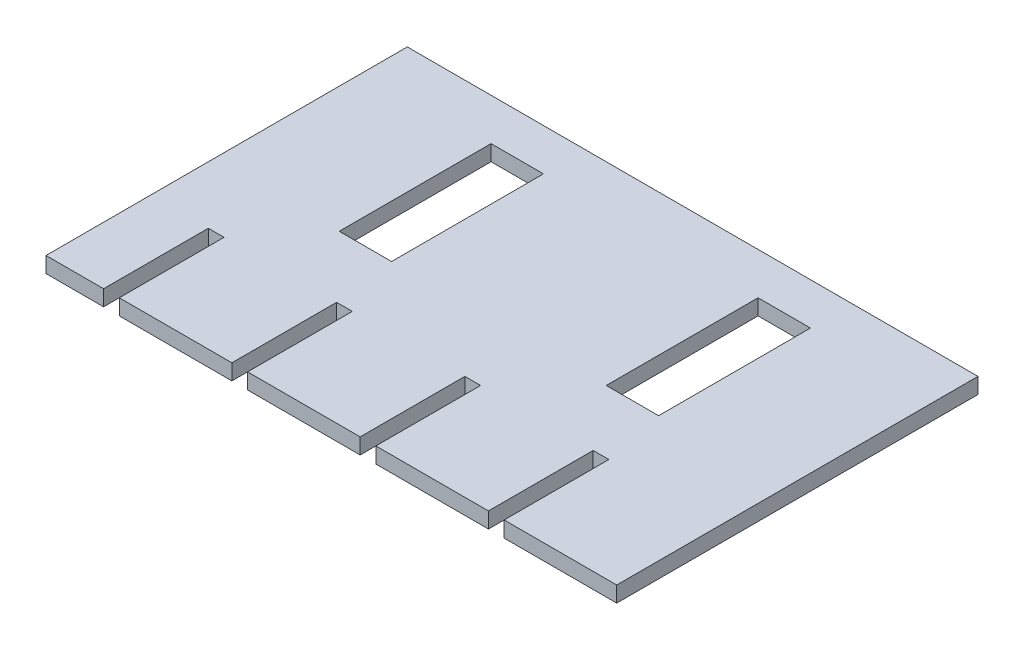
SolidWorks part; units mm, degrees
ref_plane "Front Plane" through (0, 0, 0) normal (0, 0, 1) x (1, 0, 0)
ref_plane "Top Plane" through (0, 0, 0) normal (0, 1, 0) x (1, 0, 0)
ref_plane "Right Plane" through (0, 0, 0) normal (1, 0, 0) x (0, 0, -1)
sketch "Sketch1" plane through (0, 0, 0) normal (0, 1, 0) x (1, 0, 0)
  line L1 (-27.25, 17.25) -> (27.25, 17.25)
  line L2 (-27.25, 17.25) -> (-27.25, -17.25)
  line L3 (-27.25, -17.25) -> (27.25, -17.25)
  line L4 (27.25, 17.25) -> (27.25, -17.25)
  line L5 (-27.25, 17.25) -> (27.25, -17.25) construction
  line L6 (-27.25, -17.25) -> (27.25, 17.25) construction
  point P0 (0, 0)
extrude "Boss-Extrude1" add sketch "Sketch1" along normal blind 1.5
sketch "Sketch2" plane through (0, 1.5, 0) normal (0, 1, 0) x (1, 0, 0)
  line L0 (0, 17.25) -> (0, 6)
  line L1 (27.25, 17.25) -> (-27.25, 17.25) construction
sketch "Sketch3" plane through (0, 1.5, 0) normal (0, 1, 0) x (1, 0, 0)
  line L0 (0, 6) -> (-27.25, 6)
  line L1 (-27.25, 17.25) -> (-27.25, -17.25) construction
sketch "Sketch5" plane through (0, 1.5, 0) normal (0, 1, 0) x (1, 0, 0)
  line L0 (-27.25, 6) -> (-12.75, 6)
sketch "Sketch6" plane through (0, 1.5, 0) normal (0, 1, 0) x (1, 0, 0)
  line L1 (-15.25, 13.25) -> (-10.25, 13.25)
  line L2 (-15.25, 13.25) -> (-15.25, -1.25)
  line L3 (-15.25, -1.25) -> (-10.25, -1.25)
  line L4 (-10.25, 13.25) -> (-10.25, -1.25)
  line L5 (-15.25, 13.25) -> (-10.25, -1.25) construction
  line L6 (-15.25, -1.25) -> (-10.25, 13.25) construction
  point P0 (-12.75, 6)
extrude "Cut-Extrude1" cut sketch "Sketch6" against normal blind 2
sketch "Sketch7" plane through (0, 1.5, 0) normal (0, 1, 0) x (1, 0, 0)
  line L0 (0, 6) -> (27.25, 6)
  line L1 (27.25, -17.25) -> (27.25, 17.25) construction
sketch "Sketch8" plane through (0, 1.5, 0) normal (0, 1, 0) x (1, 0, 0)
  line L0 (27.25, 6) -> (12.75, 6)
sketch "Sketch9" plane through (0, 1.5, 0) normal (0, 1, 0) x (1, 0, 0)
  line L1 (10.25, 13.25) -> (15.25, 13.25)
  line L2 (10.25, 13.25) -> (10.25, -1.25)
  line L3 (10.25, -1.25) -> (15.25, -1.25)
  line L4 (15.25, 13.25) -> (15.25, -1.25)
  line L5 (10.25, 13.25) -> (15.25, -1.25) construction
  line L6 (10.25, -1.25) -> (15.25, 13.25) construction
  point P0 (12.75, 6)
extrude "Cut-Extrude2" cut sketch "Sketch9" against normal blind 2
sketch "Sketch10" plane through (0, 1.5, 0) normal (0, 1, 0) x (1, 0, 0)
  line L0 (-27.25, -17.25) -> (-21.75, -17.25)
  line L1 (-27.25, -17.25) -> (27.25, -17.25) construction
sketch "Sketch11" plane through (0, 1.5, 0) normal (0, 1, 0) x (1, 0, 0)
  line L0 (-21.75, -17.25) -> (-20.25, -17.25)
  line L1 (-27.25, -17.25) -> (27.25, -17.25) construction
sketch "Sketch12" plane through (0, 1.5, 0) normal (0, 1, 0) x (1, 0, 0)
  line L0 (-20.25, -17.25) -> (2.75, -17.25)
  line L1 (-27.25, -17.25) -> (27.25, -17.25) construction
sketch "Sketch27" plane through (0, 1.5, 0) normal (0, 1, 0) x (1, 0, 0)
  line L0 (-21.75, -17.25) -> (-21.75, -7.25)
  line L1 (-21.75, -7.25) -> (-20.25, -7.25)
  line L2 (-20.25, -7.25) -> (-20.25, -17.25)
  line L3 (-20.25, -17.25) -> (-21.75, -17.25)
extrude "Cut-Extrude3" cut sketch "Sketch27" against normal blind 2
sketch "Sketch37" plane through (0, 1.5, 0) normal (0, 1, 0) x (1, 0, 0)
  line L0 (2.75, -17.25) -> (4.25, -17.25)
  line L1 (-20.25, -17.25) -> (27.25, -17.25) construction
  line L2 (2.75, -17.25) -> (2.75, -7.25)
  line L3 (2.75, -7.25) -> (4.25, -7.25)
  line L4 (4.25, -7.25) -> (4.25, -17.25)
extrude "Cut-Extrude10" cut sketch "Sketch37" against normal blind 2
sketch "Sketch38" plane through (0, 1.5, 0) normal (0, 1, 0) x (1, 0, 0)
  line L0 (-20.25, -17.25) -> (-9.5, -17.25)
  line L1 (-20.25, -17.25) -> (2.75, -17.25) construction
sketch "Sketch39" plane through (0, 1.5, 0) normal (0, 1, 0) x (1, 0, 0)
  line L0 (-9.5, -17.25) -> (-9.5, -7.25)
  line L1 (-9.5, -7.25) -> (-8, -7.25)
  line L2 (-8, -7.25) -> (-8, -17.25)
  line L3 (-20.25, -17.25) -> (2.75, -17.25) construction
  line L4 (-8, -17.25) -> (-9.5, -17.25)
extrude "Cut-Extrude11" cut sketch "Sketch39" against normal blind 2
sketch "Sketch40" plane through (0, 1.5, 0) normal (0, 1, 0) x (1, 0, 0)
  line L0 (4.25, -17.25) -> (15, -17.25)
  line L1 (4.25, -17.25) -> (27.25, -17.25) construction
sketch "Sketch41" plane through (0, 1.5, 0) normal (0, 1, 0) x (1, 0, 0)
  line L0 (15, -17.25) -> (15, -7.25)
  line L1 (15, -7.25) -> (16.5, -7.25)
  line L2 (16.5, -7.25) -> (16.5, -17.25)
  line L3 (4.25, -17.25) -> (27.25, -17.25) construction
  line L4 (16.5, -17.25) -> (15, -17.25)
extrude "Cut-Extrude12" cut sketch "Sketch41" against normal blind 2
